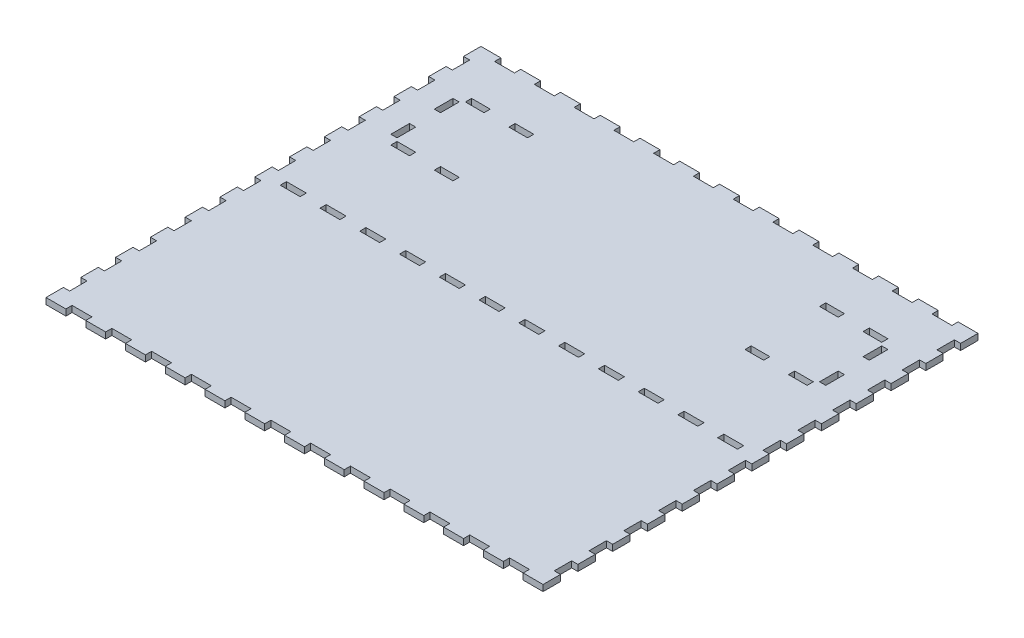
SolidWorks part; units mm, degrees
ref_plane "Plan de face" through (0, 0, 0) normal (0, 0, 1) x (1, 0, 0)
ref_plane "Plan de dessus" through (0, 0, 0) normal (0, 1, 0) x (1, 0, 0)
ref_plane "Plan de droite" through (0, 0, 0) normal (1, 0, 0) x (0, 0, -1)
sketch "Esquisse1" plane through (0, 0, 0) normal (0, 1, 0) x (1, 0, 0)
  line L1 (0, 0) -> (400, 0)
  line L2 (0, 0) -> (0, -350)
  line L3 (0, -350) -> (400, -350)
  line L4 (400, 0) -> (400, -350)
  dimension "D1" = 400
  dimension "D2" = 350
extrude "Boss.-Extru.1" add sketch "Esquisse1" along normal blind 5
ref_plane "Plan2" through (0, 0, 175) normal (0, 0, -1) x (-1, 0, 0)
ref_plane "Plan3" through (200, 0, 0) normal (1, 0, 0) x (0, 0, -1)
sketch "Esquisse2" plane through (0, 5, 0) normal (0, 1, 0) x (1, 0, 0)
  line L0 (400, 0) -> (0, 0) construction
  line L1 (16, 0) -> (32, 0)
  line L2 (16, 0) -> (16, -5)
  line L3 (16, -5) -> (32, -5)
  line L4 (32, 0) -> (32, -5)
  line L7 (0, 0) -> (400, 0) construction
  line L8 (0, 0) -> (0, -350) construction
  dimension "D1" = 400
  dimension "D2" = 16
  dimension "D3" = 16
  dimension "D4" = 5
extrude "Enlèv. mat.-Extru.1" cut sketch "Esquisse2" against normal blind 5
pattern_linear "Répétition linéaire1" count 12 spacing 32 along (1, 0, 0) of "Enlèv. mat.-Extru.1"
sketch "Esquisse3" plane through (0, 5, 0) normal (0, 1, 0) x (1, 0, 0)
  line L0 (0, 0) -> (0, -350) construction
  line L1 (0, -14) -> (5, -14)
  line L2 (0, -14) -> (0, -28)
  line L3 (0, -28) -> (5, -28)
  line L4 (5, -14) -> (5, -28)
  line L5 (0, 0) -> (0, -350) construction
  line L6 (0, -350) -> (400, -350) construction
  line L7 (16, 0) -> (0, 0) construction
  dimension "D4" = 5
  dimension "D1" = 350
  dimension "D2" = 14
  dimension "D3" = 14
extrude "Enlèv. mat.-Extru.2" cut sketch "Esquisse3" against normal blind 5
pattern_linear "Répétition linéaire2" count 12 spacing 28 along (0, 0, 1) of "Enlèv. mat.-Extru.2"
mirror "Symétrie1" about plane through (0, 0, 175) normal (0, 0, -1) of "Répétition linéaire1", "Enlèv. mat.-Extru.1"
mirror "Symétrie2" about plane through (200, 0, 0) normal (1, 0, 0) of "Répétition linéaire2", "Enlèv. mat.-Extru.2"
sketch "Esquisse4" plane through (0, 5, 0) normal (0, 1, 0) x (1, 0, 0)
  line L0 (48, 0) -> (32, 0) construction
  line L1 (32.5, -40) -> (47.5, -40)
  line L2 (32.5, -40) -> (32.5, -45)
  line L3 (32.5, -45) -> (47.5, -45)
  line L4 (47.5, -40) -> (47.5, -45)
  line L5 (67.5, -40) -> (82.5, -40)
  line L6 (67.5, -40) -> (67.5, -45)
  line L7 (67.5, -45) -> (82.5, -45)
  line L8 (82.5, -40) -> (82.5, -45)
  line L9 (32.5, -100) -> (47.5, -100)
  line L10 (32.5, -100) -> (32.5, -105)
  line L11 (32.5, -105) -> (47.5, -105)
  line L12 (47.5, -100) -> (47.5, -105)
  line L13 (67.5, -100) -> (82.5, -100)
  line L14 (67.5, -100) -> (67.5, -105)
  line L15 (67.5, -105) -> (82.5, -105)
  line L16 (82.5, -100) -> (82.5, -105)
  line L17 (47.5, -45) -> (67.5, -100) construction
  line L18 (67.5, -45) -> (47.5, -100) construction
  line L19 (200, -2.75) -> (200, 2.75) construction
  line L20 (57.5, -72.5) -> (-23.7594, -72.5) construction
  line L21 (30, -47.5) -> (25, -47.5)
  line L22 (30, -47.5) -> (30, -62.5)
  line L23 (30, -62.5) -> (25, -62.5)
  line L24 (25, -47.5) -> (25, -62.5)
  line L25 (25, -82.5) -> (30, -82.5)
  line L26 (25, -82.5) -> (25, -97.5)
  line L27 (25, -97.5) -> (30, -97.5)
  line L28 (30, -82.5) -> (30, -97.5)
  point P18 (57.5, -72.5)
  dimension "D1" = 5
  dimension "D2" = 15
  dimension "D4" = 15
  dimension "D5" = 20
  dimension "D7" = 5
  dimension "D11" = 55
  dimension "D12" = 40
  dimension "D13" = 142.5
  dimension "D14" = 175
  dimension "D15" = 5
  dimension "D3" = 15
  dimension "D6" = 15
  dimension "D8" = 20
  dimension "D9" = 10
extrude "Enlèv. mat.-Extru.3" cut sketch "Esquisse4" against normal blind 5
mirror "Symétrie3" about plane through (200, 0, 0) normal (1, 0, 0) of "Enlèv. mat.-Extru.3"
sketch "Esquisse5" plane through (0, 5, 0) normal (0, 1, 0) x (1, 0, 0)
  line L0 (16, 0) -> (16, -5) construction
  line L1 (16, -172.5) -> (32, -172.5)
  line L2 (16, -172.5) -> (16, -177.5)
  line L3 (16, -177.5) -> (32, -177.5)
  line L4 (32, -172.5) -> (32, -177.5)
  line L5 (32, -5) -> (32, 0) construction
  line L6 (32, -175) -> (16, -175) construction
  line L7 (2.75, -175) -> (-2.75, -175) construction
  dimension "D1" = 5
extrude "Enlèv. mat.-Extru.4" cut sketch "Esquisse5" against normal blind 10
pattern_linear "Répétition linéaire3" count 12 spacing 32 along (1, 0, 0) of "Enlèv. mat.-Extru.4"
equation "\"D2@Esquisse2\"=\"D1@Esquisse2\"/25"
equation "\"D3@Esquisse2\"=\"D2@Esquisse2\""
equation "\"D4@Répétition linéaire1\"=\"D2@Esquisse2\"*2"
equation "\"D3@Répétition linéaire1\"=\"D2@Esquisse2\"*2"
equation "\"D2@Esquisse3\"=\"D1@Esquisse3\"/25"
equation "\"D3@Esquisse3\"=\"D2@Esquisse3\""
equation "\"D3@Répétition linéaire2\"=\"D2@Esquisse3\"*2"
equation "\"D4@Esquisse4\"=\"D2@Esquisse4\""
equation "\"D7@Esquisse4\"=\"D1@Esquisse4\""
equation "\"D13@Esquisse4\"=285/2"
equation "\"D14@Esquisse4\"=350/2"
equation "\"D15@Esquisse4\"=\"D1@Esquisse4\""
equation "\"D3@Esquisse4\"=\"D2@Esquisse4\""
equation "\"D6@Esquisse4\"=\"D2@Esquisse4\""
equation "\"D8@Esquisse4\"=\"D5@Esquisse4\""
equation "\"D9@Esquisse4\"=\"D8@Esquisse4\"/2"
